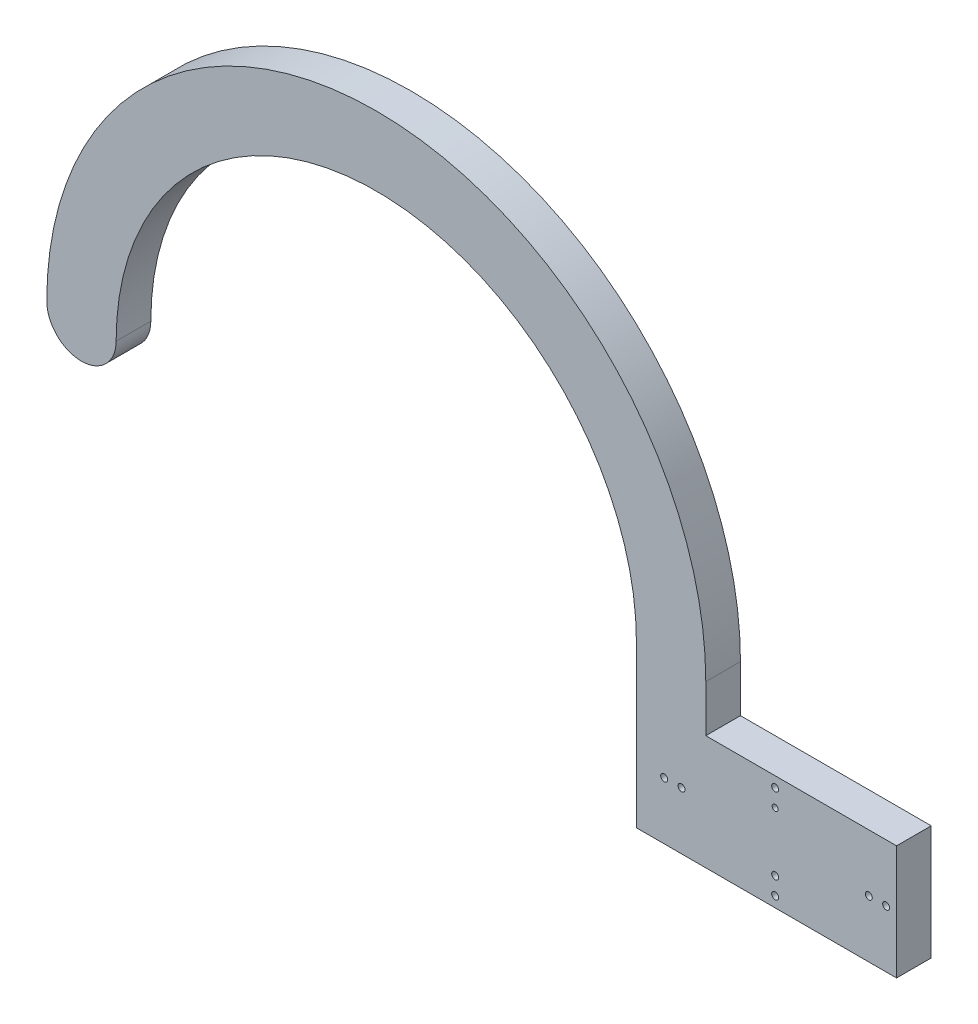
SolidWorks part; units mm, degrees
ref_plane "Front Plane" through (0, 0, 0) normal (0, 0, 1) x (1, 0, 0)
ref_plane "Top Plane" through (0, 0, 0) normal (0, 1, 0) x (1, 0, 0)
ref_plane "Right Plane" through (0, 0, 0) normal (1, 0, 0) x (0, 0, -1)
sketch "Sketch1" plane through (0, 0, 0) normal (0, 0, 1) x (1, 0, 0)
  line L13 (95, -8.25) -> (95, -6.75)
  line L14 (95, -8.25) -> (95, -10.75)
  line L15 (85, 0) -> (85, -6.75)
  line L16 (112.5002, -23.25) -> (77.4998, -23.25)
  line L17 (112.5002, -23.25) -> (112.5002, -6.75)
  line L18 (112.5002, -6.75) -> (85, -6.75)
  line L20 (112.5002, -15) -> (108.5002, -15)
  line L21 (111.0002, -14.5) -> (111.0002, -15.5)
  line L22 (75, 0) -> (75, -23.25)
  line L23 (75, -23.25) -> (77.4998, -23.25)
  line L24 (95.5, -8.25) -> (94.5, -8.25)
  line L25 (108.5002, -14.5) -> (108.5002, -15.5)
  line L26 (95.5, -19.23) -> (94.5, -19.23)
  line L27 (95.5, -21.73) -> (94.5, -21.73)
  line L28 (81.5002, -14.5) -> (81.5002, -15.5)
  line L29 (95, -18.73) -> (95, -23.25)
  line L30 (79.0002, -14.5) -> (79.0002, -15.5)
  line L31 (81.5002, -15) -> (75, -15)
  arc A0 (0, 0) -> (75, 0) centre (37.5, 0) cw
  arc A1 (-10, 0) -> (85, 0) centre (37.5, 0) cw
  arc A2 (-10, 0) -> (0, 0) centre (-5, 0) ccw
  circle A4 centre (95, -8.25) radius 0.5
  circle A5 centre (95, -10.75) radius 0.4297
  circle A6 centre (95, -21.73) radius 0.5
  circle A8 centre (95, -19.23) radius 0.5
  circle A9 centre (111.0002, -15) radius 0.5
  circle A10 centre (108.5002, -15) radius 0.5
  circle A11 centre (81.5002, -15) radius 0.5
  circle A12 centre (79.0002, -15) radius 0.5
  dimension "D1" = 75
  dimension "D2" = 95
  dimension "D3" = 10
  dimension "D4" = 10
  dimension "D5" = 1.5
  dimension "D6" = 16.5
  dimension "D7" = 1.5
  dimension "D8" = 1
  dimension "D9" = 2.5
  dimension "D10" = 1
  dimension "D11" = 1
  dimension "D12" = 2.5
  dimension "D13" = 1.52
  dimension "D14" = 20
  dimension "D15" = 20
  dimension "D16" = 1
  dimension "D17" = 2.5
  dimension "D18" = 1
  dimension "D19" = 1
  dimension "D20" = 1
  dimension "D21" = 2.5
  dimension "D22" = 32
extrude "Boss-Extrude1" add sketch "Sketch1" along normal blind 5
